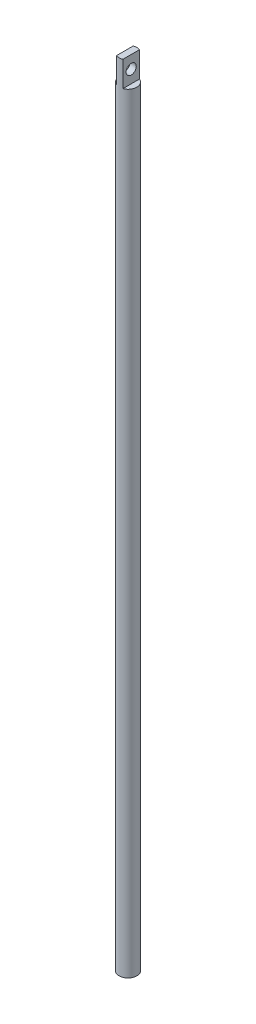
SolidWorks part; units mm, degrees
ref_plane "前视基准面" through (0, 0, 0) normal (0, 0, 1) x (1, 0, 0)
ref_plane "上视基准面" through (0, 0, 0) normal (0, 1, 0) x (1, 0, 0)
ref_plane "右视基准面" through (0, 0, 0) normal (1, 0, 0) x (0, 0, -1)
sketch "草图1" plane through (0, 0, 0) normal (0, 1, 0) x (1, 0, 0)
  circle A0 centre (0, 0) radius 7
  dimension "D1" = 14
extrude "凸台-拉伸1" add sketch "草图1" along normal blind 15
sketch "草图2" plane through (0, 15, 0) normal (0, 1, 0) x (1, 0, 0)
  circle A0 centre (0, 0) radius 7
  dimension "D1" = 14
extrude "凸台-拉伸2" add sketch "草图2" along normal blind 610
sketch "草图3" plane through (0, 625, 0) normal (0, 1, 0) x (1, 0, 0)
  line L1 (-2.5, 10) -> (2.5, 10)
  line L2 (-2.5, 10) -> (-2.5, -10)
  line L3 (-2.5, -10) -> (2.5, -10)
  line L4 (2.5, 10) -> (2.5, -10)
  line L5 (-2.5, 10) -> (2.5, -10) construction
  line L6 (-2.5, -10) -> (2.5, 10) construction
  point P0 (0, 0)
  point P1 (0, 0)
  dimension "D1" = 5
  dimension "D2" = 20
extrude "切除-拉伸1" cut sketch "草图3" against normal blind 20 flip side to cut
ref_plane "基准面1" through (-2.5, 0, 0) normal (-1, 0, 0) x (0, 0, 1)
sketch "草图4" plane through (-2.5, 0, 0) normal (-1, 0, 0) x (0, 0, 1)
  line L0 (0, 0) -> (0, 362.7684) construction
  line L4 (-6.5383, 615) -> (6.5383, 615)
  line L5 (-6.5383, 615) -> (4.3704, 615) construction
  circle A0 centre (0, 615) radius 4
  point P8 (0, 615)
  dimension "D2" = 8
  dimension "D1" = 10
extrude "切除-拉伸2" cut sketch "草图4" against normal blind 20
